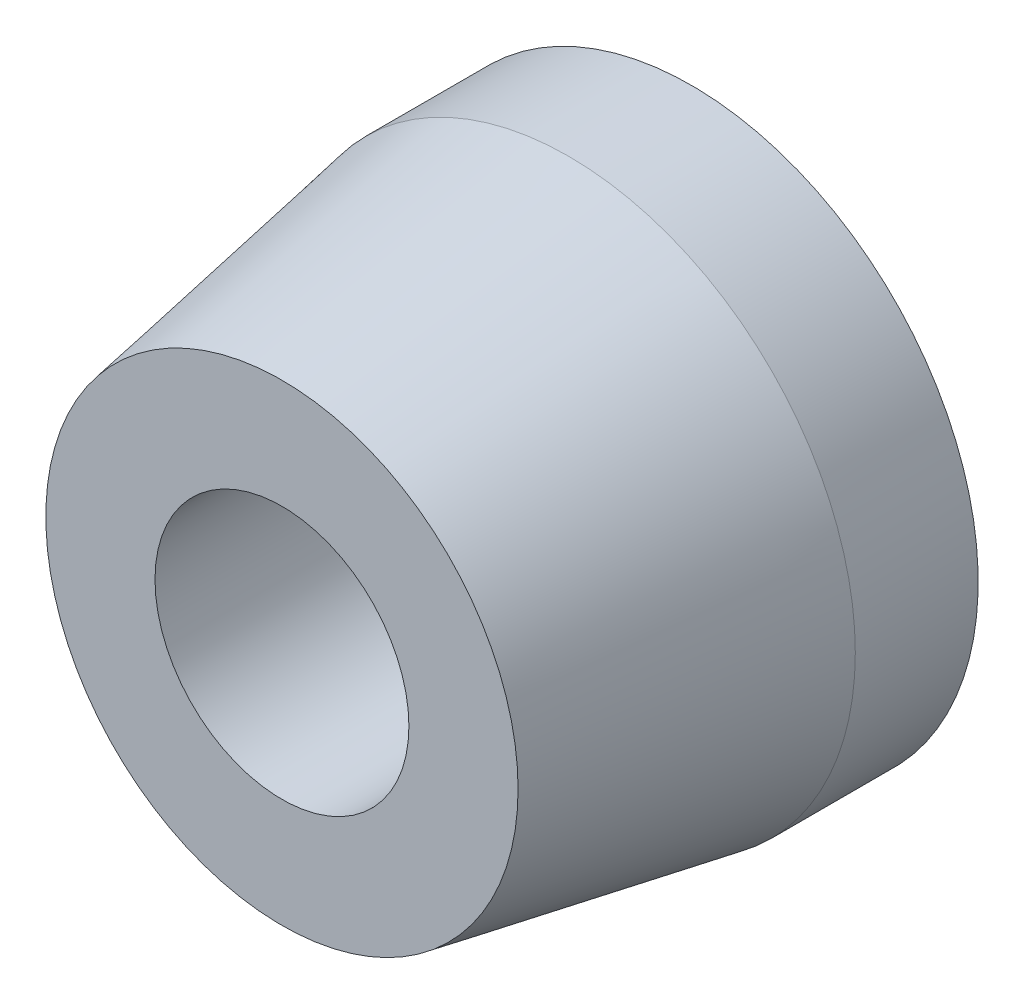
SolidWorks part; units mm, degrees
ref_plane "Front Plane" through (0, 0, 0) normal (0, 0, 1) x (1, 0, 0)
ref_plane "Top Plane" through (0, 0, 0) normal (0, 1, 0) x (1, 0, 0)
ref_plane "Right Plane" through (0, 0, 0) normal (1, 0, 0) x (0, 0, -1)
sketch "Sketch1" plane through (0, 0, 0) normal (0, 0, 1) x (1, 0, 0)
  circle A0 centre (0, 0) radius 7
extrude "Boss-Extrude1" add sketch "Sketch1" along normal blind 7 draft 10
sketch "Sketch2" plane through (0, 0, 7) normal (0, 0, 1) x (1, 0, 0)
  circle A0 centre (0, 0) radius 3.1
extrude "Cut-Extrude1" cut sketch "Sketch2" against normal up to surface (7 mm away) up to face at (7, 0, 0)
sketch "Sketch3" plane through (0, 0, 0) normal (0, 0, -1) x (-1, 0, 0)
  circle A0 centre (0, 0) radius 7
  circle A1 centre (0, 0) radius 1.65
extrude "Boss-Extrude2" add sketch "Sketch3" along normal blind 3
sketch "Sketch4" plane through (0, 0, -3) normal (0, 0, -1) x (-1, 0, 0)
  circle A0 centre (0, 0) radius 1.65
  circle A1 centre (0, 0) radius 2.5
extrude "Boss-Extrude3" add sketch "Sketch4" along normal blind 1.8
